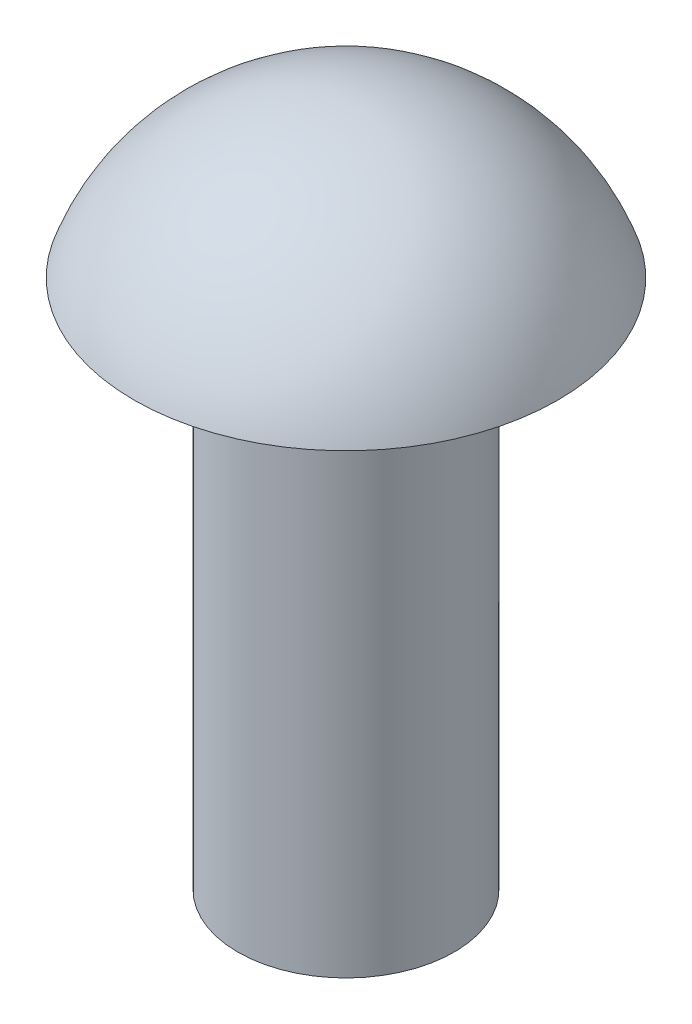
SolidWorks part; units mm, degrees
material "1060 Alloy"
ref_plane "Front Plane" through (0, 0, 0) normal (0, 0, 1) x (1, 0, 0)
ref_plane "Top Plane" through (0, 0, 0) normal (0, 1, 0) x (1, 0, 0)
ref_plane "Right Plane" through (0, 0, 0) normal (1, 0, 0) x (0, 0, -1)
sketch "Sketch1" plane through (0, 0, 0) normal (1, 0, 0) x (0, 0, -1)
  line L0 (0, 0) -> (0, -7.7) construction
  line L1 (0, -7.7) -> (1.225, -7.7)
  line L2 (1.225, -7.7) -> (1.225, -1.7)
  line L3 (1.225, -1.7) -> (2.4, -1.7)
  line L6 (0, 0) -> (0, -7.7)
  arc A0 (2.4, -1.7) -> (0, 0) centre (0, -2.5441) ccw
  point P7 (0, -2.0725)
  point P8 (0, -2.5332)
  point P12 (0, -0.8892)
  point P13 (10.6854, -6.8392)
  point P14 (0, -3.7896)
  point P15 (0, -3.491)
  point P16 (0, 0)
  point P18 (2.5965, -1.4)
  dimension "D4" = 2.4
  dimension "D1" = 2.45
  dimension "D2" = 6
  dimension "D3" = 1.7
revolve "Revolve2" add sketch "Sketch1" angle 360 about L0
